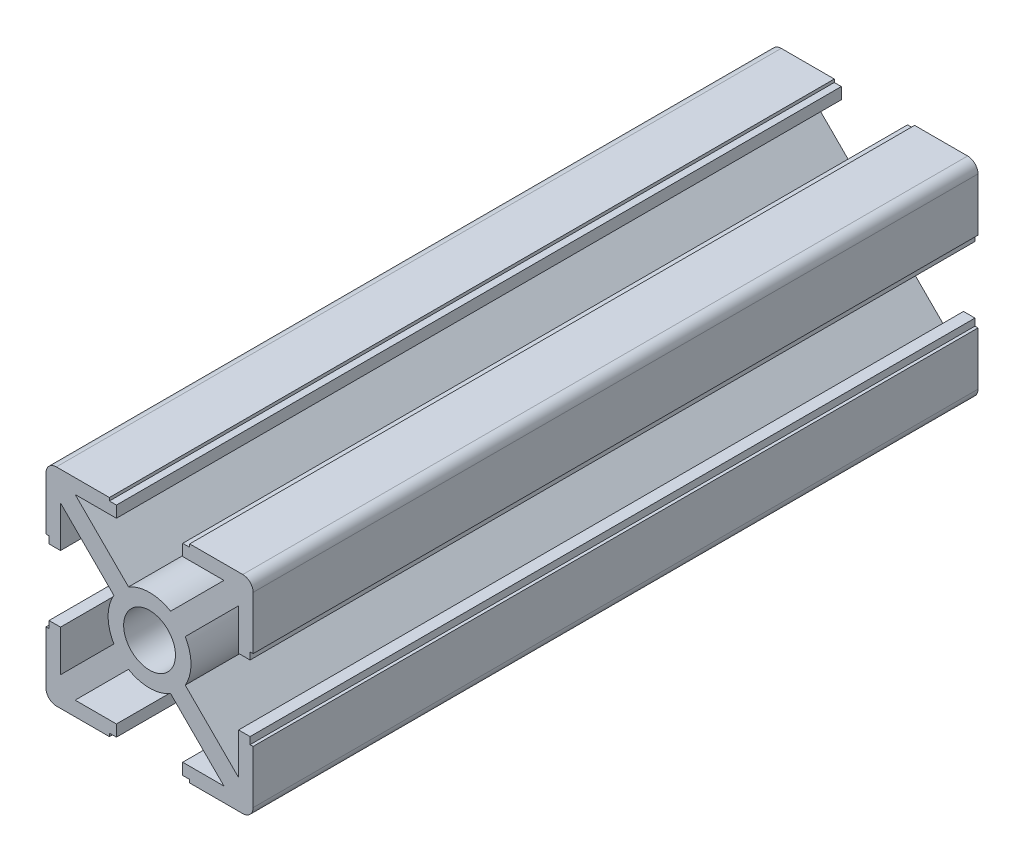
SolidWorks part; units mm, degrees
material "1060 Alloy"
ref_plane "Ön Düzlem" through (0, 0, 0) normal (0, 0, 1) x (1, 0, 0)
ref_plane "Üst Düzlem" through (0, 0, 0) normal (0, 1, 0) x (1, 0, 0)
ref_plane "Sağ Düzlem" through (0, 0, 0) normal (1, 0, 0) x (0, 0, -1)
sketch "Sketch1" plane through (0, 0, 0) normal (0, 0, 1) x (1, 0, 0)
  line L0 (-9.7071, -3.2) -> (-8.6, -3.2)
  line L2 (-10, -3.8775) -> (-10, -9)
  line L3 (-9, -10) -> (-3.8775, -10)
  line L5 (-10, -3.8775) -> (-9.7071, -3.8775)
  line L6 (-10, -10) -> (-9.7071, -9.7071) construction
  line L9 (-3.2, -8.6) -> (-7.1858, -8.6)
  line L10 (-8.6, -3.2) -> (-8.6, -7.1858)
  line L13 (-7.1858, -8.6) -> (-2.0315, -3.4457)
  line L14 (-8.6, -7.1858) -> (-3.4457, -2.0315)
  line L15 (-10.7071, -9.2929) -> (9.2929, 10.7071) construction
  line L16 (-9.2929, -10.7071) -> (10.7071, 9.2929) construction
  line L18 (-10, -10) -> (10, 10) construction
  line L19 (-2.5, 0) -> (-9.7071, 0) construction
  line L20 (0, -2.5) -> (0, -6.9362) construction
  line L21 (-3.2, -8.6) -> (-3.2, -9.7071)
  line L23 (-9.7071, -3.8775) -> (-9.7071, -3.2)
  line L24 (-3.2, -9.7071) -> (-3.8775, -9.7071)
  line L25 (-3.8775, -9.7071) -> (-3.8775, -10)
  line L28 (10, -10) -> (9.7071, -9.7071) construction
  line L30 (3.8775, -9.7071) -> (3.8775, -10)
  line L31 (3.2, -9.7071) -> (3.8775, -9.7071)
  line L32 (9.7071, -3.8775) -> (9.7071, -3.2)
  line L33 (3.2, -8.6) -> (3.2, -9.7071)
  line L34 (8.6, -7.1858) -> (3.4457, -2.0315)
  line L35 (7.1858, -8.6) -> (2.0315, -3.4457)
  line L36 (8.6, -3.2) -> (8.6, -7.1858)
  line L37 (3.2, -8.6) -> (7.1858, -8.6)
  line L38 (10, -3.8775) -> (9.7071, -3.8775)
  line L39 (9, -10) -> (3.8775, -10)
  line L40 (10, -3.8775) -> (10, -9)
  line L41 (9.7071, -3.2) -> (8.6, -3.2)
  line L42 (10, 10) -> (9.7071, 9.7071) construction
  line L43 (0, 2.5) -> (0, 6.9362) construction
  line L44 (-10, 10) -> (-9.7071, 9.7071) construction
  line L45 (9.7071, 3.2) -> (8.6, 3.2)
  line L46 (10, 3.8775) -> (10, 9)
  line L47 (9, 10) -> (3.8775, 10)
  line L48 (10, 3.8775) -> (9.7071, 3.8775)
  line L49 (3.2, 8.6) -> (7.1858, 8.6)
  line L50 (8.6, 3.2) -> (8.6, 7.1858)
  line L51 (7.1858, 8.6) -> (2.0315, 3.4457)
  line L52 (8.6, 7.1858) -> (3.4457, 2.0315)
  line L53 (3.2, 8.6) -> (3.2, 9.7071)
  line L54 (9.7071, 3.8775) -> (9.7071, 3.2)
  line L55 (3.2, 9.7071) -> (3.8775, 9.7071)
  line L56 (3.8775, 9.7071) -> (3.8775, 10)
  line L57 (-3.8775, 9.7071) -> (-3.8775, 10)
  line L58 (-3.2, 9.7071) -> (-3.8775, 9.7071)
  line L59 (-9.7071, 3.8775) -> (-9.7071, 3.2)
  line L60 (-3.2, 8.6) -> (-3.2, 9.7071)
  line L61 (-8.6, 7.1858) -> (-3.4457, 2.0315)
  line L62 (-7.1858, 8.6) -> (-2.0315, 3.4457)
  line L63 (-8.6, 3.2) -> (-8.6, 7.1858)
  line L64 (-3.2, 8.6) -> (-7.1858, 8.6)
  line L65 (-10, 3.8775) -> (-9.7071, 3.8775)
  line L66 (-9, 10) -> (-3.8775, 10)
  line L67 (-10, 3.8775) -> (-10, 9)
  line L68 (-9.7071, 3.2) -> (-8.6, 3.2)
  arc A2 (-10, -9) -> (-9, -10) centre (-9, -9) ccw
  arc A3 (-2.0315, -3.4457) -> (2.0315, -3.4457) centre (0, 0) ccw
  arc A4 (-3.4457, 2.0315) -> (-3.4457, -2.0315) centre (0, 0) ccw
  circle A5 centre (0, 0) radius 2.5
  arc A6 (3.4457, 2.0315) -> (3.4457, -2.0315) centre (0, 0) cw
  arc A7 (10, -9) -> (9, -10) centre (9, -9) cw
  arc A8 (10, 9) -> (9, 10) centre (9, 9) ccw
  arc A9 (-2.0315, 3.4457) -> (2.0315, 3.4457) centre (0, 0) cw
  arc A10 (-10, 9) -> (-9, 10) centre (-9, 9) cw
  dimension "D10" = 1
  dimension "D5" = 1.4
  dimension "D6" = 1.4
  dimension "D7" = 3.2
  dimension "D11" = 3.2
  dimension "D8" = 1
  dimension "D9" = 1
extrude "Boss-Extrude1" add sketch "Sketch1" along normal blind 70
